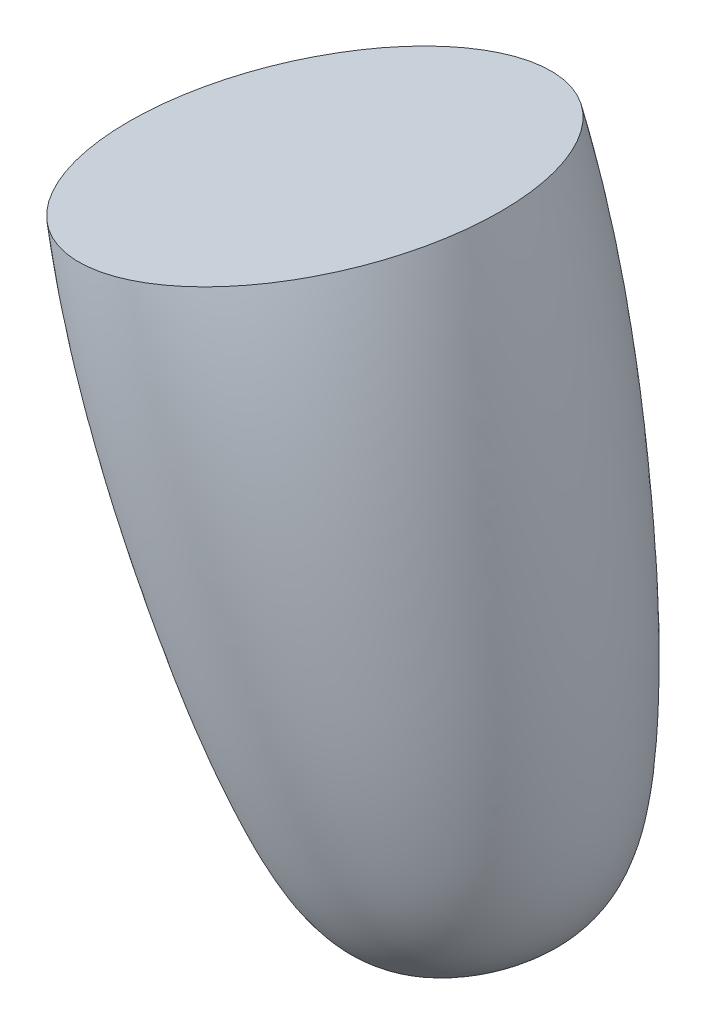
SolidWorks part; units mm, degrees
ref_plane "Alzado" through (0, 0, 0) normal (0, 0, 1) x (1, 0, 0)
ref_plane "Planta" through (0, 0, 0) normal (0, 1, 0) x (1, 0, 0)
ref_plane "Vista lateral" through (0, 0, 0) normal (1, 0, 0) x (0, 0, -1)
sketch "Croquis1" plane through (0, 0, 0) normal (0, 0, 1) x (1, 0, 0)
  line L0 (-105.1062, 41.2676) -> (-88.3931, -16.3577) construction
  line L1 (-123.3542, 35.9751) -> (-79.2097, 48.7784) construction
  line L2 (-123.3542, 35.9751) -> (-105.1062, 41.2676)
  line L3 (-105.1062, 41.2676) -> (-88.3931, -16.3577)
  line L4 (-123.3542, 35.9751) -> (-123.3542, 105.9751) construction
  line L5 (-123.3542, 105.9751) -> (-97.9444, 105.9751) construction
  spline S0 degree 3 poles (-123.3542, 35.9751) (-121.1664, 25.7462) (-115.745, 10.8575) (-106.1279, -9.3915) (-97.5268, -20.7909) (-88.3931, -16.3577) knots 0 0 0 0 0.457844 0.674368 1 1 1 1
  dimension "D2" = 70
  dimension "D1" = 60
  dimension "D3" = 19
revolve "Revolución1" add sketch "Croquis1" angle 360 about L3
